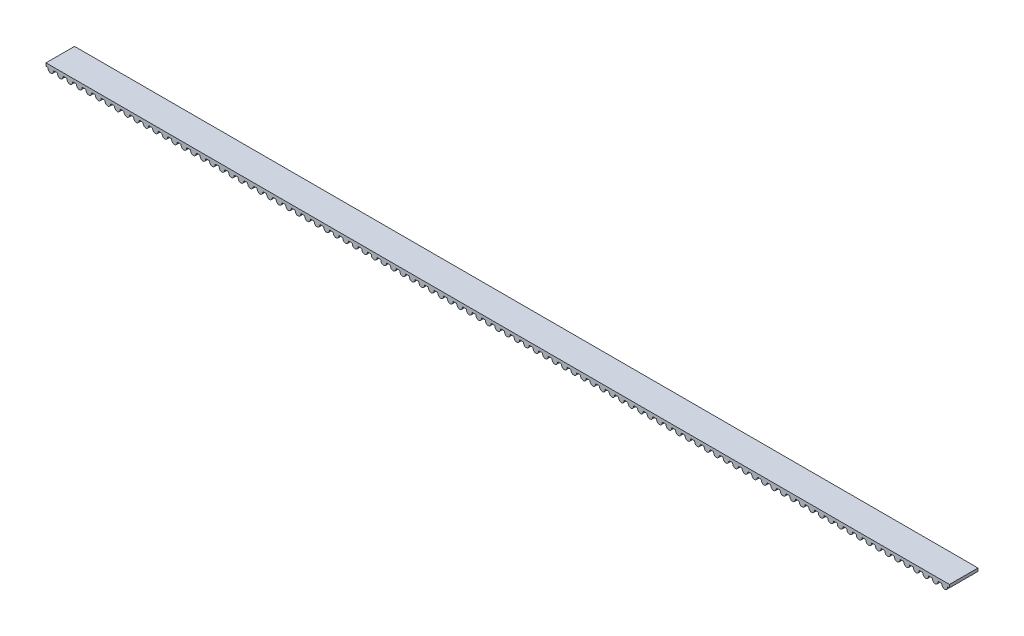
SolidWorks part; units mm, degrees
ref_plane "Plan de face" through (0, 0, 0) normal (0, 0, 1) x (1, 0, 0)
ref_plane "Plan de dessus" through (0, 0, 0) normal (0, 1, 0) x (1, 0, 0)
ref_plane "Plan de droite" through (0, 0, 0) normal (1, 0, 0) x (0, 0, -1)
sketch "Sketch1" plane through (0, 0, 0) normal (0, 0, 1) x (1, 0, 0)
  line L0 (0, 0) -> (30, 0)
  line L1 (0, -0.63) -> (0.2611, -0.63)
  line L2 (1, -1.38) -> (1, -0.825) construction
  line L3 (2, -0.63) -> (1.7389, -0.63)
  line L4 (1, -1.38) -> (1.8227, -1.38) construction
  line L5 (2, -0.63) -> (2.2611, -0.63)
  line L6 (4, -0.63) -> (3.7389, -0.63)
  line L7 (4, -0.63) -> (4.2611, -0.63)
  line L8 (6, -0.63) -> (5.7389, -0.63)
  line L9 (6, -0.63) -> (6.2611, -0.63)
  line L10 (8, -0.63) -> (7.7389, -0.63)
  line L11 (8, -0.63) -> (8.2611, -0.63)
  line L12 (10, -0.63) -> (9.7389, -0.63)
  line L13 (10, -0.63) -> (10.2611, -0.63)
  line L14 (12, -0.63) -> (11.7389, -0.63)
  line L15 (12, -0.63) -> (12.2611, -0.63)
  line L16 (14, -0.63) -> (13.7389, -0.63)
  line L17 (14, -0.63) -> (14.2611, -0.63)
  line L18 (16, -0.63) -> (15.7389, -0.63)
  line L19 (16, -0.63) -> (16.2611, -0.63)
  line L20 (18, -0.63) -> (17.7389, -0.63)
  line L21 (18, -0.63) -> (18.2611, -0.63)
  line L22 (20, -0.63) -> (19.7389, -0.63)
  line L23 (20, -0.63) -> (20.2611, -0.63)
  line L24 (22, -0.63) -> (21.7389, -0.63)
  line L25 (22, -0.63) -> (22.2611, -0.63)
  line L26 (24, -0.63) -> (23.7389, -0.63)
  line L27 (24, -0.63) -> (24.2611, -0.63)
  line L28 (26, -0.63) -> (25.7389, -0.63)
  line L29 (26, -0.63) -> (26.2611, -0.63)
  line L30 (28, -0.63) -> (27.7389, -0.63)
  line L31 (28, -0.63) -> (28.2611, -0.63)
  line L32 (30, -0.63) -> (29.7389, -0.63)
  line L33 (0, 0) -> (0, -0.63)
  line L34 (30, 0) -> (30, -0.63)
  arc A0 (0.2611, -0.63) -> (0.4099, -0.7609) centre (0.2611, -0.78) cw
  arc A1 (0.4099, -0.7609) -> (0.499, -1.0637) centre (1.4017, -0.6336) ccw
  arc A2 (0.499, -1.0637) -> (1.501, -1.0637) centre (1, -0.825) ccw
  arc A3 (1.5901, -0.7609) -> (1.501, -1.0637) centre (0.5983, -0.6336) cw
  arc A4 (1.7389, -0.63) -> (1.5901, -0.7609) centre (1.7389, -0.78) ccw
  arc A5 (2.2611, -0.63) -> (2.4099, -0.7609) centre (2.2611, -0.78) cw
  arc A6 (2.4099, -0.7609) -> (2.499, -1.0637) centre (3.4017, -0.6336) ccw
  arc A7 (2.499, -1.0637) -> (3.501, -1.0637) centre (3, -0.825) ccw
  arc A8 (3.5901, -0.7609) -> (3.501, -1.0637) centre (2.5983, -0.6336) cw
  arc A9 (3.7389, -0.63) -> (3.5901, -0.7609) centre (3.7389, -0.78) ccw
  arc A10 (4.2611, -0.63) -> (4.4099, -0.7609) centre (4.2611, -0.78) cw
  arc A11 (4.4099, -0.7609) -> (4.499, -1.0637) centre (5.4017, -0.6336) ccw
  arc A12 (4.499, -1.0637) -> (5.501, -1.0637) centre (5, -0.825) ccw
  arc A13 (5.5901, -0.7609) -> (5.501, -1.0637) centre (4.5983, -0.6336) cw
  arc A14 (5.7389, -0.63) -> (5.5901, -0.7609) centre (5.7389, -0.78) ccw
  arc A15 (6.2611, -0.63) -> (6.4099, -0.7609) centre (6.2611, -0.78) cw
  arc A16 (6.4099, -0.7609) -> (6.499, -1.0637) centre (7.4017, -0.6336) ccw
  arc A17 (6.499, -1.0637) -> (7.501, -1.0637) centre (7, -0.825) ccw
  arc A18 (7.5901, -0.7609) -> (7.501, -1.0637) centre (6.5983, -0.6336) cw
  arc A19 (7.7389, -0.63) -> (7.5901, -0.7609) centre (7.7389, -0.78) ccw
  arc A20 (8.2611, -0.63) -> (8.4099, -0.7609) centre (8.2611, -0.78) cw
  arc A21 (8.4099, -0.7609) -> (8.499, -1.0637) centre (9.4017, -0.6336) ccw
  arc A22 (8.499, -1.0637) -> (9.501, -1.0637) centre (9, -0.825) ccw
  arc A23 (9.5901, -0.7609) -> (9.501, -1.0637) centre (8.5983, -0.6336) cw
  arc A24 (9.7389, -0.63) -> (9.5901, -0.7609) centre (9.7389, -0.78) ccw
  arc A25 (10.2611, -0.63) -> (10.4099, -0.7609) centre (10.2611, -0.78) cw
  arc A26 (10.4099, -0.7609) -> (10.499, -1.0637) centre (11.4017, -0.6336) ccw
  arc A27 (10.499, -1.0637) -> (11.501, -1.0637) centre (11, -0.825) ccw
  arc A28 (11.5901, -0.7609) -> (11.501, -1.0637) centre (10.5983, -0.6336) cw
  arc A29 (11.7389, -0.63) -> (11.5901, -0.7609) centre (11.7389, -0.78) ccw
  arc A30 (12.2611, -0.63) -> (12.4099, -0.7609) centre (12.2611, -0.78) cw
  arc A31 (12.4099, -0.7609) -> (12.499, -1.0637) centre (13.4017, -0.6336) ccw
  arc A32 (12.499, -1.0637) -> (13.501, -1.0637) centre (13, -0.825) ccw
  arc A33 (13.5901, -0.7609) -> (13.501, -1.0637) centre (12.5983, -0.6336) cw
  arc A34 (13.7389, -0.63) -> (13.5901, -0.7609) centre (13.7389, -0.78) ccw
  arc A35 (14.2611, -0.63) -> (14.4099, -0.7609) centre (14.2611, -0.78) cw
  arc A36 (14.4099, -0.7609) -> (14.499, -1.0637) centre (15.4017, -0.6336) ccw
  arc A37 (14.499, -1.0637) -> (15.501, -1.0637) centre (15, -0.825) ccw
  arc A38 (15.5901, -0.7609) -> (15.501, -1.0637) centre (14.5983, -0.6336) cw
  arc A39 (15.7389, -0.63) -> (15.5901, -0.7609) centre (15.7389, -0.78) ccw
  arc A40 (16.2611, -0.63) -> (16.4099, -0.7609) centre (16.2611, -0.78) cw
  arc A41 (16.4099, -0.7609) -> (16.499, -1.0637) centre (17.4017, -0.6336) ccw
  arc A42 (16.499, -1.0637) -> (17.501, -1.0637) centre (17, -0.825) ccw
  arc A43 (17.5901, -0.7609) -> (17.501, -1.0637) centre (16.5983, -0.6336) cw
  arc A44 (17.7389, -0.63) -> (17.5901, -0.7609) centre (17.7389, -0.78) ccw
  arc A45 (18.2611, -0.63) -> (18.4099, -0.7609) centre (18.2611, -0.78) cw
  arc A46 (18.4099, -0.7609) -> (18.499, -1.0637) centre (19.4017, -0.6336) ccw
  arc A47 (18.499, -1.0637) -> (19.501, -1.0637) centre (19, -0.825) ccw
  arc A48 (19.5901, -0.7609) -> (19.501, -1.0637) centre (18.5983, -0.6336) cw
  arc A49 (19.7389, -0.63) -> (19.5901, -0.7609) centre (19.7389, -0.78) ccw
  arc A50 (20.2611, -0.63) -> (20.4099, -0.7609) centre (20.2611, -0.78) cw
  arc A51 (20.4099, -0.7609) -> (20.499, -1.0637) centre (21.4017, -0.6336) ccw
  arc A52 (20.499, -1.0637) -> (21.501, -1.0637) centre (21, -0.825) ccw
  arc A53 (21.5901, -0.7609) -> (21.501, -1.0637) centre (20.5983, -0.6336) cw
  arc A54 (21.7389, -0.63) -> (21.5901, -0.7609) centre (21.7389, -0.78) ccw
  arc A55 (22.2611, -0.63) -> (22.4099, -0.7609) centre (22.2611, -0.78) cw
  arc A56 (22.4099, -0.7609) -> (22.499, -1.0637) centre (23.4017, -0.6336) ccw
  arc A57 (22.499, -1.0637) -> (23.501, -1.0637) centre (23, -0.825) ccw
  arc A58 (23.5901, -0.7609) -> (23.501, -1.0637) centre (22.5983, -0.6336) cw
  arc A59 (23.7389, -0.63) -> (23.5901, -0.7609) centre (23.7389, -0.78) ccw
  arc A60 (24.2611, -0.63) -> (24.4099, -0.7609) centre (24.2611, -0.78) cw
  arc A61 (24.4099, -0.7609) -> (24.499, -1.0637) centre (25.4017, -0.6336) ccw
  arc A62 (24.499, -1.0637) -> (25.501, -1.0637) centre (25, -0.825) ccw
  arc A63 (25.5901, -0.7609) -> (25.501, -1.0637) centre (24.5983, -0.6336) cw
  arc A64 (25.7389, -0.63) -> (25.5901, -0.7609) centre (25.7389, -0.78) ccw
  arc A65 (26.2611, -0.63) -> (26.4099, -0.7609) centre (26.2611, -0.78) cw
  arc A66 (26.4099, -0.7609) -> (26.499, -1.0637) centre (27.4017, -0.6336) ccw
  arc A67 (26.499, -1.0637) -> (27.501, -1.0637) centre (27, -0.825) ccw
  arc A68 (27.5901, -0.7609) -> (27.501, -1.0637) centre (26.5983, -0.6336) cw
  arc A69 (27.7389, -0.63) -> (27.5901, -0.7609) centre (27.7389, -0.78) ccw
  arc A70 (28.2611, -0.63) -> (28.4099, -0.7609) centre (28.2611, -0.78) cw
  arc A71 (28.4099, -0.7609) -> (28.499, -1.0637) centre (29.4017, -0.6336) ccw
  arc A72 (28.499, -1.0637) -> (29.501, -1.0637) centre (29, -0.825) ccw
  arc A73 (29.5901, -0.7609) -> (29.501, -1.0637) centre (28.5983, -0.6336) cw
  arc A74 (29.7389, -0.63) -> (29.5901, -0.7609) centre (29.7389, -0.78) ccw
  point P10 (3, -1.38)
  dimension "D1" = 0.15
  dimension "D2" = 1
  dimension "D3" = 0.555
  dimension "D4" = 0.4017
  dimension "D5" = 0.75
  dimension "D6" = 1
  dimension "D7" = 1.38
  dimension "D9" = 0.2611
extrude "Boss-Extrude1" add sketch "Sketch1" along normal blind 6 contours L0 L34 L32 A74 A73 A72 A71 A70 L31 L30 A69 A68 A67 A66 A65 L29 L28 A64 A63 A62 A61 A60 L27 L26 A59 A58 A57 A56 A55 L25 L24 A54 A53 A52 A51 A50 L23 L22 A49 A48 A47 A46 A45 L21 L20 A44 A43 A42 A41 A40 L19 L18 A39 A38 A37 A36 A35 L17 L16 A34 A33 A32 A31 A30 L15 L14 A29 A28 A27 A26 A25 L13 L12 A24 A23 A22 A21 A20 L11 L10 A19 A18 A17 A16 A15 L9 L8 A14 A13 A12 A11 A10 L7 L6 A9 A8 A7 A6 A5 L5 L3 A4 A3 A2 A1 A0 L1 L33
mirror "Mirror1" about plane through (30, 0, 6) normal (1, 0, 0) of "Boss-Extrude1"
pattern_linear "LPattern2" count 14 spacing 10 along (-1, 0, 0) of "Boss-Extrude1"
